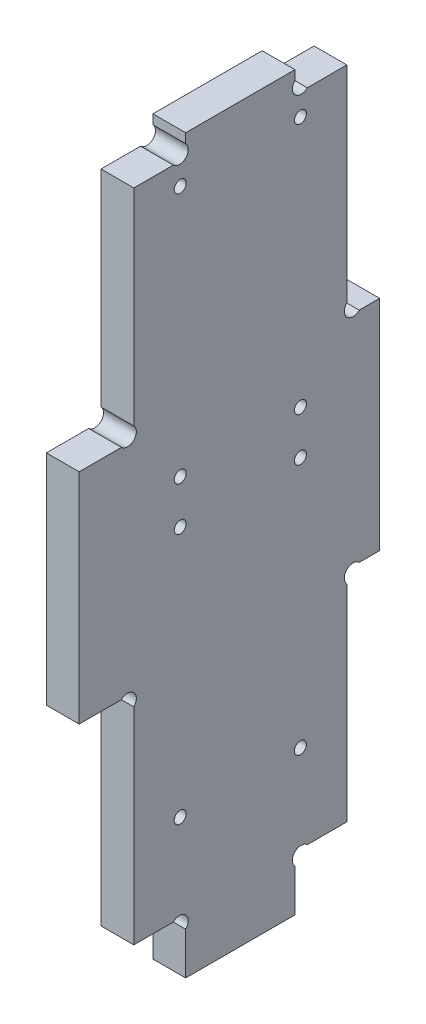
SolidWorks part; units mm, degrees
ref_plane "Plan de face" through (0, 0, 0) normal (0, 0, 1) x (1, 0, 0)
ref_plane "Plan de dessus" through (0, 0, 0) normal (0, 1, 0) x (1, 0, 0)
ref_plane "Plan de droite" through (0, 0, 0) normal (1, 0, 0) x (0, 0, -1)
sketch "Esquisse1" plane through (0, 0, 0) normal (1, 0, 0) x (0, 0, -1)
  line L0 (-6.665, 0) -> (102.6681, 0) construction
  line L1 (0, -6.466) -> (0, 166.4589) construction
  line L2 (6.406, 134) -> (102.6681, 134) construction
  line L3 (19.5, -6.466) -> (19.5, 140.5689) construction
  line L4 (55, 166.4589) -> (55, -6.466) construction
  line L5 (10, 5.4571) -> (10, 140.5689) construction
  line L6 (6.406, 10) -> (82.7567, 10) construction
  line L7 (-6.665, 130) -> (82.7567, 130) construction
  line L8 (-6.665, 70) -> (82.7567, 70) construction
  line L9 (-6.665, 50) -> (60.1633, 50) construction
  line L10 (29.5, 150.2484) -> (29.5, -6.466) construction
  line L11 (49, 140.5689) -> (49, 5.4571) construction
  line L12 (49, 50) -> (63.6844, 35.3156) construction
  line L13 (19.5, 7.7373) -> (19.5, 0)
  line L14 (10, 50) -> (-12.528, 27.472) construction
  line L15 (17.2373, 10) -> (10, 10)
  line L16 (19.5, 10) -> (3.3898, -6.1102) construction
  line L17 (51.2627, 50) -> (55, 50)
  line L18 (7.7373, 50) -> (0, 50)
  line L19 (39.5, 7.7373) -> (39.5, 0)
  line L20 (51.2627, 90) -> (55, 90)
  line L21 (7.7373, 90) -> (0, 90)
  line L22 (19.5, 0) -> (39.5, 0)
  line L23 (41.7627, 10) -> (49, 10)
  line L24 (49, 10) -> (49, 47.7373)
  line L25 (10, 10) -> (10, 47.7373)
  line L26 (55, 90) -> (55, 50)
  line L27 (0, 50) -> (0, 90)
  line L28 (19.5, 130) -> (7.338, 142.162) construction
  line L29 (19.5, 132.2627) -> (19.5, 134)
  line L30 (39.5, 132.2627) -> (39.5, 134)
  line L31 (10, 92.2627) -> (10, 130)
  line L32 (10, 130) -> (17.2373, 130)
  line L33 (19.5, 134) -> (39.5, 134)
  line L34 (41.7627, 130) -> (49, 130)
  line L35 (49, 130) -> (49, 92.2627)
  line L36 (52, 79.6313) -> (52, 62.1476) construction
  line L37 (5, 81.2768) -> (5, 66.1586) construction
  line L38 (18.5, 132.2627) -> (18.5, 72.081) construction
  line L39 (-6.665, 76) -> (59.3937, 76) construction
  line L40 (14.5, 132.2627) -> (14.5, 72.081) construction
  line L41 (44.5, 132.2626) -> (44.5, 73.2647) construction
  line L42 (11.2207, 80) -> (23.6055, 80) construction
  line L43 (21.1467, 126) -> (2.7518, 126) construction
  arc A0 (51.2627, 50) -> (49, 47.7373) centre (50.1314, 48.8686) ccw
  arc A1 (10, 47.7373) -> (7.7373, 50) centre (8.8686, 48.8686) ccw
  arc A2 (19.5, 7.7373) -> (17.2373, 10) centre (18.3686, 8.8686) ccw
  arc A3 (39.5, 7.7373) -> (41.7627, 10) centre (40.6314, 8.8686) cw
  arc A4 (10, 92.2627) -> (7.7373, 90) centre (8.8686, 91.1314) cw
  arc A5 (51.2627, 90) -> (49, 92.2627) centre (50.1314, 91.1314) cw
  arc A6 (17.2373, 130) -> (19.5, 132.2627) centre (18.3686, 131.1314) ccw
  arc A7 (41.7627, 130) -> (39.5, 132.2627) centre (40.6314, 131.1314) cw
  circle A8 centre (18.5, 126) radius 1.1
  circle A9 centre (18.5, 80) radius 1.1
  circle A10 centre (40.5, 126) radius 1.1
  circle A11 centre (40.5, 80) radius 1.1
  circle A12 centre (18.5, 72) radius 1.1
  circle A13 centre (40.5, 72) radius 1.1
  circle A14 centre (40.5, 26) radius 1.1
  circle A15 centre (18.5, 26) radius 1.1
  dimension "D14" = 45
  dimension "D15" = 3
  dimension "D17" = 30
  dimension "D1" = 55
  dimension "D2" = 134
  dimension "D3" = 10
  dimension "D4" = 4
  dimension "D5" = 60
  dimension "D6" = 20
  dimension "D7" = 10
  dimension "D8" = 6
  dimension "D9" = 19.5
  dimension "D10" = 10
  dimension "D11" = 45
  dimension "D12" = 45
  dimension "D13" = 45
  dimension "D16" = 5
  dimension "D18" = 54
  dimension "D19" = 15
  dimension "D20" = 4
  dimension "D21" = 4
  dimension "D22" = 4
extrude "Extrusion1" add sketch "Esquisse1" along normal blind 6
